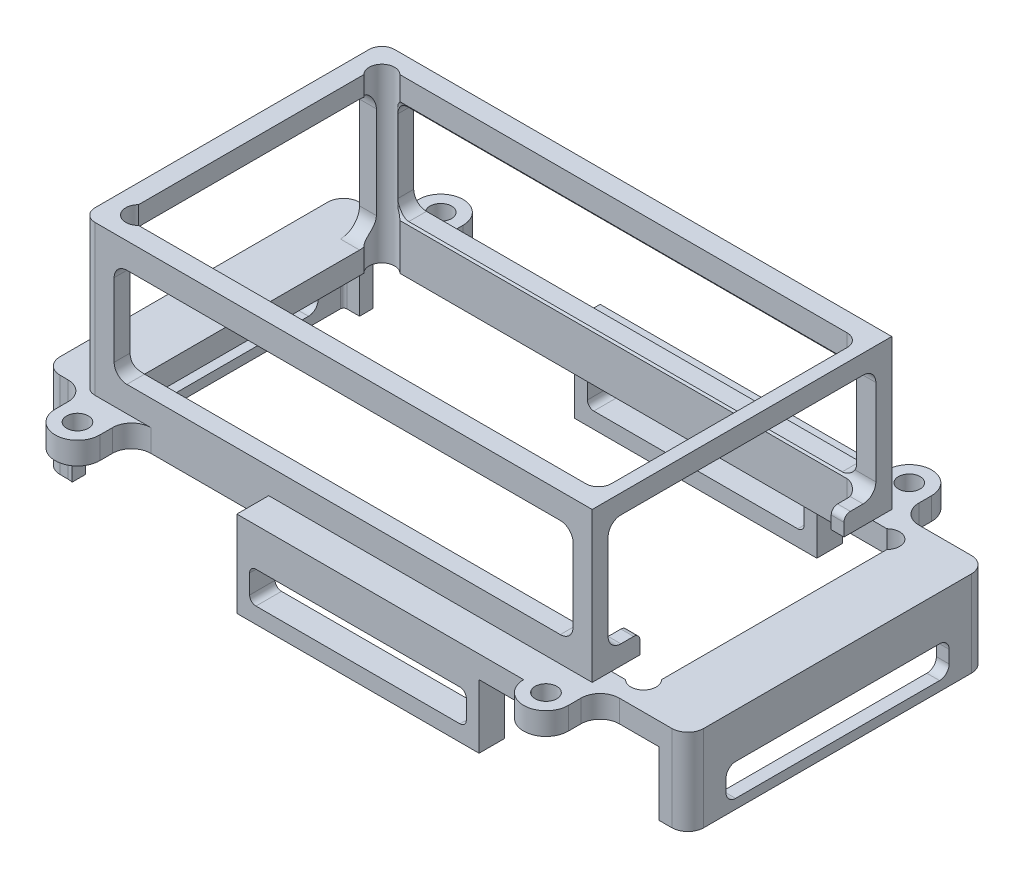
SolidWorks part; units mm, degrees
material "AISI 1035 钢 (SS)"
ref_plane "前视基准面" through (0, 0, 0) normal (0, 0, 1) x (1, 0, 0)
ref_plane "上视基准面" through (0, 0, 0) normal (0, 1, 0) x (1, 0, 0)
ref_plane "右视基准面" through (0, 0, 0) normal (1, 0, 0) x (0, 0, -1)
sketch "草图1" plane through (0, 0, 0) normal (0, 1, 0) x (1, 0, 0)
  line L0 (-34.1716, -20.5) -> (36, -20.5)
  line L1 (-38, 23.5) -> (40, 23.5)
  line L2 (-40, 21.5) -> (-40, -21.5)
  line L3 (-38, -23.5) -> (40, -23.5)
  line L4 (40, 23.5) -> (40, -23.5)
  line L5 (-40, 23.5) -> (40, -23.5) construction
  line L6 (-40, -23.5) -> (40, 23.5) construction
  line L7 (-37, -20.5) -> (37, -20.5) construction
  line L8 (-34.1716, 20.5) -> (36, 20.5)
  line L9 (-37, 17.6716) -> (-37, -17.6716)
  line L10 (37, 20.5) -> (37, -20.5) construction
  line L11 (-6.6939, 3.9327) -> (38, -20.5) construction
  line L12 (-6.6939, -3.9327) -> (0.5, 0) construction
  line L13 (38, -18.5) -> (38, 18.5)
  line L14 (-37, 20.5) -> (37, 20.5) construction
  line L15 (-37, -20.5) -> (-35.5858, -19.0858) construction
  line L16 (0, 0) -> (-3.1731, 0) construction
  line L17 (-37, 20.5) -> (-37, -20.5) construction
  line L18 (-40, -23.5) -> (40, -23.5) construction
  line L19 (-40, 23.5) -> (-40, -23.5) construction
  line L20 (-40, 23.5) -> (40, 23.5) construction
  arc A0 (36, -20.5) -> (38, -18.5) centre (36, -18.5) ccw
  arc A1 (38, 18.5) -> (36, 20.5) centre (36, 18.5) ccw
  arc A2 (-37, -17.6716) -> (-34.1716, -20.5) centre (-35.5858, -19.0858) ccw
  arc A3 (-37, 17.6716) -> (-34.1716, 20.5) centre (-35.5858, 19.0858) cw
  arc A4 (-38, -23.5) -> (-40, -21.5) centre (-38, -21.5) cw
  arc A5 (-38, 23.5) -> (-40, 21.5) centre (-38, 21.5) ccw
  point P0 (0, 0)
  point P16 (38, 20.5)
  dimension "D5" = 2
  dimension "D8" = 4
  dimension "D9" = 2
  dimension "D1" = 80
  dimension "D2" = 47
  dimension "D4" = 2
  dimension "D6" = 45
  dimension "D7" = 2
  dimension "D3" = 3
extrude "凸台-拉伸1" add sketch "草图1" along normal blind 23.5
sketch "草图2" plane through (0, 0, 0) normal (0, -1, 0) x (1, 0, 0)
  line L0 (1, 23.5) -> (1, -23.5) construction
  line L1 (-38, 23.5) -> (40, 23.5) construction
  line L2 (40, -23.5) -> (-38, -23.5) construction
  line L3 (37.75, 0) -> (-35.75, 0) construction
  line L4 (37.75, 28.5) -> (37.75, -28.5) construction
  line L5 (40, 0) -> (55, 0) construction
  line L6 (40, 23.5) -> (40, -23.5) construction
  line L7 (55, 0) -> (-46, 0) construction
  line L8 (55, 0) -> (55, 23.5)
  line L9 (55, 23.5) -> (41.25, 23.5)
  line L10 (-46, 23.5) -> (-46, -23.5)
  line L11 (-46, -23.5) -> (-39.25, -23.5)
  line L12 (55, -23.5) -> (55, 0)
  line L13 (-34.1716, 20.5) -> (36, 20.5) construction
  line L14 (5.4444, -0.4555) -> (5.4444, 0.4555) construction
  line L15 (-34.1716, 20.5) -> (42.2319, 20.5)
  line L16 (34.25, 23.5) -> (-32.25, 23.5)
  line L17 (42.2319, -20.5) -> (-34.1716, -20.5)
  line L18 (47, -20.5) -> (-38, 20.5) construction
  line L19 (47, 20.5) -> (-38, -20.5) construction
  line L20 (37.75, 18.5) -> (37.75, 28.5) construction
  line L21 (34.25, 23.5) -> (34.25, 28.5)
  line L22 (41.25, -23.5) -> (41.25, -28.5)
  line L23 (41.25, 23.5) -> (41.25, 28.5)
  line L24 (34.25, -23.5) -> (34.25, -28.5)
  line L25 (-32.25, -23.5) -> (-32.25, -28.5)
  line L26 (-39.25, -23.5) -> (-39.25, -28.5)
  line L27 (-39.25, 23.5) -> (-39.25, 28.5)
  line L28 (-32.25, 23.5) -> (-32.25, 28.5)
  line L29 (-37, -17.6716) -> (-37, 17.6716)
  line L30 (45.0603, -14.2439) -> (-37, -14.2439) construction
  line L31 (4.0302, -14.2439) -> (4.0302, -22.3158) construction
  line L32 (45.0603, 17.6716) -> (45.0603, -17.6716)
  line L33 (41.25, -23.5) -> (55, -23.5)
  line L34 (-32.25, -23.5) -> (34.25, -23.5)
  line L35 (-39.25, 23.5) -> (-46, 23.5)
  circle A0 centre (37.75, 28.5) radius 1.7
  arc A1 (41.25, -28.5) -> (34.25, -28.5) centre (37.75, -28.5) cw
  arc A2 (41.25, 28.5) -> (34.25, 28.5) centre (37.75, 28.5) ccw
  circle A3 centre (37.75, -28.5) radius 1.7
  arc A4 (-39.25, -28.5) -> (-32.25, -28.5) centre (-35.75, -28.5) ccw
  circle A5 centre (-35.75, -28.5) radius 1.7
  arc A6 (-39.25, 28.5) -> (-32.25, 28.5) centre (-35.75, 28.5) cw
  circle A7 centre (-35.75, 28.5) radius 1.7
  arc A8 (-37, -17.6716) -> (-34.1716, -20.5) centre (-35.5858, -19.0858) ccw construction
  arc A9 (-34.1716, 20.5) -> (-37, 17.6716) centre (-35.5858, 19.0858) ccw construction
  arc A10 (-37, -17.6716) -> (-34.1716, -20.5) centre (-35.5858, -19.0858) ccw
  arc A11 (-34.1716, 20.5) -> (-37, 17.6716) centre (-35.5858, 19.0858) ccw
  arc A12 (42.2319, 20.5) -> (45.0603, 17.6716) centre (43.6461, 19.0858) cw
  arc A13 (45.0603, -17.6716) -> (42.2319, -20.5) centre (43.6461, -19.0858) cw
  point P6 (1, 0)
  point P18 (4.5, 0)
  point P31 (37.75, 23.5)
  dimension "D3" = 3.4
  dimension "D1" = 73.5
  dimension "D2" = 57
  dimension "D4" = 15
  dimension "D5" = 101
  dimension "D6" = 85
extrude "凸台-拉伸2" add sketch "草图2" along normal blind 3.5
fillet "圆角1" radius 2.5 4 edges at (-46, -1.75, 23.5) (-46, -1.75, -23.5) (55, -1.75, -23.5) (55, -1.75, 23.5)
sketch "草图3" plane through (0, -3.5, 0) normal (0, -1, 0) x (1, 0, 0)
  line L0 (55, -21) -> (55, 21) construction
  line L1 (55, -21) -> (55, 21)
  line L2 (52.5, -23.5) -> (50.5, -23.5)
  line L3 (41.25, -23.5) -> (52.5, -23.5) construction
  line L4 (52.5, 23.5) -> (50.5, 23.5)
  line L5 (52.5, 23.5) -> (41.25, 23.5) construction
  line L6 (-46, 21) -> (-46, -21) construction
  line L7 (-46, 21) -> (-46, -21)
  line L8 (-43.5, -23.5) -> (-41.5, -23.5)
  line L9 (-43.5, -23.5) -> (-39.25, -23.5) construction
  line L10 (-41.5, 23.5) -> (-43.5, 23.5)
  arc A0 (52.5, -23.5) -> (55, -21) centre (52.5, -21) ccw construction
  arc A1 (55, 21) -> (52.5, 23.5) centre (52.5, 21) ccw construction
  arc A2 (52.5, -23.5) -> (55, -21) centre (52.5, -21) ccw
  arc A3 (55, 21) -> (52.5, 23.5) centre (52.5, 21) ccw
  arc A4 (-43.5, 23.5) -> (-46, 21) centre (-43.5, 21) ccw construction
  arc A5 (-46, -21) -> (-43.5, -23.5) centre (-43.5, -21) ccw construction
  arc A6 (-43.5, 23.5) -> (-46, 21) centre (-43.5, 21) ccw
  arc A7 (-46, -21) -> (-43.5, -23.5) centre (-43.5, -21) ccw
  dimension "D1" = 2
  dimension "D2" = 2
  dimension "D3" = 2
  dimension "D4" = 2
extrude "拉伸-薄壁1" add sketch "草图3" along normal blind 10 thin thin type one direction reverse wall 2
sketch "草图4" plane through (-40, 0, 0) normal (-1, 0, 0) x (0, 0, 1)
  line L0 (0, 0) -> (0, 20.5) construction
  line L3 (-21.5, 0) -> (21.5, 0) construction
  line L4 (-21.5, 23.5) -> (21.5, 23.5) construction
  line L6 (17, 0) -> (-17, 0)
  line L7 (20, 3) -> (20, 17.5)
  line L8 (17, 20.5) -> (-17, 20.5)
  line L9 (-20, 3) -> (-20, 17.5)
  line L10 (20, 0) -> (-20, 20.5) construction
  line L11 (20, 20.5) -> (-20, 0) construction
  arc A0 (-17, 0) -> (-20, 3) centre (-17, 3) cw
  arc A1 (-20, 17.5) -> (-17, 20.5) centre (-17, 17.5) cw
  arc A2 (17, 20.5) -> (20, 17.5) centre (17, 17.5) cw
  arc A3 (17, 0) -> (20, 3) centre (17, 3) ccw
  point P6 (0, 11.75)
  point P7 (0, 10.25)
  dimension "D3" = 3
  dimension "D1" = 3
  dimension "D2" = 40
extrude "切除-拉伸1" cut sketch "草图4" against normal up to next
sketch "草图5" plane through (0, 0, -23.5) normal (0, 0, -1) x (-1, 0, 0)
  line L0 (-1, 23.5) -> (-1, 19.5) construction
  line L1 (-40, 23.5) -> (38, 23.5) construction
  line L2 (-40, 11.75) -> (-37, 11.75) construction
  line L3 (-40, 23.5) -> (-40, 0) construction
  line L4 (-37, 11.75) -> (-37, 17.5)
  line L5 (-35, 19.5) -> (33, 19.5)
  line L6 (38, 23.5) -> (38, 0) construction
  line L7 (-37, 11.75) -> (-37, 6)
  line L8 (-35, 4) -> (33, 4)
  line L9 (35, 6) -> (35, 17.5)
  arc A0 (-37, 6) -> (-35, 4) centre (-35, 6) ccw
  arc A1 (-37, 17.5) -> (-35, 19.5) centre (-35, 17.5) cw
  arc A2 (33, 19.5) -> (35, 17.5) centre (33, 17.5) cw
  arc A3 (33, 4) -> (35, 6) centre (33, 6) ccw
  point P16 (-37, 4)
  point P21 (35, 19.5)
  dimension "D5" = 2
  dimension "D1" = 4
  dimension "D2" = 3
  dimension "D3" = 3
  dimension "D4" = 7.75
extrude "切除-拉伸2" cut sketch "草图5" against normal up to surface (47 mm away) up to face at (1, 5, 23.5)
sketch "草图6" plane through (40, 0, 0) normal (1, 0, 0) x (0, 0, -1)
  line L0 (0, 23.5) -> (0, 20.5) construction
  line L1 (-23.5, 23.5) -> (23.5, 23.5) construction
  line L2 (23.5, 11.75) -> (21, 11.75) construction
  line L3 (23.5, 23.5) -> (23.5, 0) construction
  line L4 (21, 5) -> (21, 18.5)
  line L5 (19, 20.5) -> (-19, 20.5)
  line L6 (0, 20.5) -> (0, 7.2335) construction
  line L7 (-21, 5) -> (-21, 18.5)
  line L8 (19, 3) -> (17, 3)
  line L9 (0, 3) -> (0, 0) construction
  line L10 (-20.5, 0) -> (20.5, 0) construction
  line L11 (16, 2) -> (16, 0)
  line L12 (-16, 2) -> (-16, 0)
  line L13 (16, 0) -> (-16, 0)
  line L14 (-17, 3) -> (-19, 3)
  arc A0 (-21, 18.5) -> (-19, 20.5) centre (-19, 18.5) cw
  arc A1 (19, 20.5) -> (21, 18.5) centre (19, 18.5) cw
  arc A2 (-21, 5) -> (-19, 3) centre (-19, 5) ccw
  arc A3 (19, 3) -> (21, 5) centre (19, 5) ccw
  arc A4 (-17, 3) -> (-16, 2) centre (-17, 2) cw
  arc A5 (16, 2) -> (17, 3) centre (17, 2) cw
  point P14 (-21, 11.75)
  point P17 (-21, 20.5)
  point P20 (21, 20.5)
  point P23 (-21, 3)
  point P26 (21, 3)
  point P37 (-16, 3)
  dimension "D3" = 2
  dimension "D6" = 1
  dimension "D1" = 3
  dimension "D2" = 2.5
  dimension "D4" = 16
  dimension "D5" = 16
extrude "切除-拉伸3" cut sketch "草图6" against normal up to next
sketch "草图7" plane through (53, 0, 0) normal (-1, 0, 0) x (0, 0, 1)
  line L0 (0, -3.5) -> (0, -13.5) construction
  line L1 (-21, -3.5) -> (21, -3.5) construction
  line L2 (-21, -13.5) -> (21, -13.5) construction
  line L4 (16, -12) -> (-16, -12)
  line L5 (17.5, -10.5) -> (17.5, -8.5)
  line L6 (16, -7) -> (-16, -7)
  line L7 (-17.5, -10.5) -> (-17.5, -8.5)
  line L8 (17.5, -12) -> (-17.5, -7) construction
  line L9 (17.5, -7) -> (-17.5, -12) construction
  arc A0 (-16, -7) -> (-17.5, -8.5) centre (-16, -8.5) ccw
  arc A1 (-17.5, -10.5) -> (-16, -12) centre (-16, -10.5) ccw
  arc A2 (16, -7) -> (17.5, -8.5) centre (16, -8.5) cw
  arc A3 (16, -12) -> (17.5, -10.5) centre (16, -10.5) ccw
  point P6 (0, -9.5)
  point P7 (0, -9.5)
  dimension "D4" = 1.5
  dimension "D1" = 4
  dimension "D2" = 35
  dimension "D3" = 5
extrude "切除-拉伸4" cut sketch "草图7" against normal blind 3.5
sketch "草图8" plane through (-44, 0, 0) normal (1, 0, 0) x (0, 0, -1)
  line L0 (0, -3.5) -> (0, -13.5) construction
  line L1 (-21, -3.5) -> (21, -3.5) construction
  line L2 (-21, -13.5) -> (21, -13.5) construction
  line L4 (16, -12) -> (-16, -12)
  line L5 (17.5, -10.5) -> (17.5, -8.5)
  line L6 (16, -7) -> (-16, -7)
  line L7 (-17.5, -10.5) -> (-17.5, -8.5)
  line L8 (17.5, -12) -> (-17.5, -7) construction
  line L9 (17.5, -7) -> (-17.5, -12) construction
  arc A0 (-16, -12) -> (-17.5, -10.5) centre (-16, -10.5) cw
  arc A1 (-17.5, -8.5) -> (-16, -7) centre (-16, -8.5) cw
  arc A2 (16, -7) -> (17.5, -8.5) centre (16, -8.5) cw
  arc A3 (16, -12) -> (17.5, -10.5) centre (16, -10.5) ccw
  point P6 (0, -9.5)
  point P7 (0, -9.5)
  dimension "D4" = 1.5
  dimension "D1" = 4
  dimension "D2" = 35
  dimension "D3" = 5
extrude "切除-拉伸5" cut sketch "草图8" against normal up to next
sketch "草图9" plane through (0, 0, 23.5) normal (0, 0, 1) x (1, 0, 0)
  line L0 (34.25, -3.5) -> (34.25, 0)
  line L1 (34.25, 0) -> (-10.75, 0)
  line L2 (-10.75, 0) -> (-10.75, -3.5)
  line L3 (34.25, -3.5) -> (-32.25, -3.5) construction
  line L4 (-10.75, -3.5) -> (34.25, -3.5)
  dimension "D1" = 45
extrude "凸台-拉伸3" add sketch "草图9" along normal blind 5
sketch "草图10" plane through (0, 0, -23.5) normal (0, 0, -1) x (-1, 0, 0)
  line L0 (-34.25, -3.5) -> (10.75, -3.5)
  line L1 (32.25, -3.5) -> (-34.25, -3.5) construction
  line L2 (-34.25, -3.5) -> (-34.25, 0)
  line L3 (-34.25, 0) -> (10.75, 0)
  line L4 (10.75, 0) -> (10.75, -3.5)
  dimension "D1" = 45
extrude "凸台-拉伸4" add sketch "草图10" along normal blind 5
sketch "草图11" plane through (0, -3.5, 0) normal (0, -1, 0) x (1, 0, 0)
  line L0 (-10.75, -28.5) -> (-10.75, -24.5)
  line L1 (-10.75, -28.5) -> (-10.75, -23.5) construction
  line L2 (-10.75, -24.5) -> (27.25, -24.5)
  line L3 (27.25, -24.5) -> (27.25, -28.5)
  line L4 (34.25, -28.5) -> (-10.75, -28.5) construction
  line L5 (27.25, -28.5) -> (-10.75, -28.5)
  line L6 (-10.75, 28.5) -> (-10.75, 24.5)
  line L7 (-10.75, 28.5) -> (-10.75, 23.5) construction
  line L8 (-10.75, 24.5) -> (27.25, 24.5)
  line L9 (27.25, 24.5) -> (27.25, 28.5)
  line L10 (-10.75, 28.5) -> (34.25, 28.5) construction
  line L11 (27.25, 28.5) -> (-10.75, 28.5)
  dimension "D1" = 4
  dimension "D2" = 38
  dimension "D3" = 4
  dimension "D4" = 38
extrude "凸台-拉伸5" add sketch "草图11" along normal up to surface (10 mm away) up to face at (-43.4369, -13.5, 0)
sketch "草图12" plane through (0, 0, 28.5) normal (0, 0, 1) x (1, 0, 0)
  line L0 (27.25, -8.5) -> (-10.75, -8.5) construction
  line L1 (27.25, -13.5) -> (27.25, -3.5) construction
  line L2 (-10.75, 0) -> (-10.75, -13.5) construction
  line L3 (27.25, -13.5) -> (-10.75, -13.5) construction
  line L5 (24.25, -11) -> (-7.75, -11)
  line L6 (25.25, -10) -> (25.25, -7)
  line L7 (24.25, -6) -> (-7.75, -6)
  line L8 (-8.75, -10) -> (-8.75, -7)
  line L9 (25.25, -11) -> (-8.75, -6) construction
  line L10 (25.25, -6) -> (-8.75, -11) construction
  arc A0 (-8.75, -7) -> (-7.75, -6) centre (-7.75, -7) cw
  arc A1 (-8.75, -10) -> (-7.75, -11) centre (-7.75, -10) ccw
  arc A2 (24.25, -6) -> (25.25, -7) centre (24.25, -7) cw
  arc A3 (24.25, -11) -> (25.25, -10) centre (24.25, -10) ccw
  point P8 (8.25, -8.5)
  dimension "D4" = 1
  dimension "D1" = 5
  dimension "D2" = 34
  dimension "D3" = 5
extrude "切除-拉伸6" cut sketch "草图12" against normal up to surface (57 mm away) up to face at (16.9167, -5.6667, -28.5)
fillet "圆角3" radius 3 6 edges at (-39.25, -1.75, 23.5) (-32.25, -1.75, 23.5) (41.25, -1.75, 23.5) (41.25, -1.75, -23.5) (-39.25, -1.75, -23.5) (-32.25, -1.75, -23.5)
